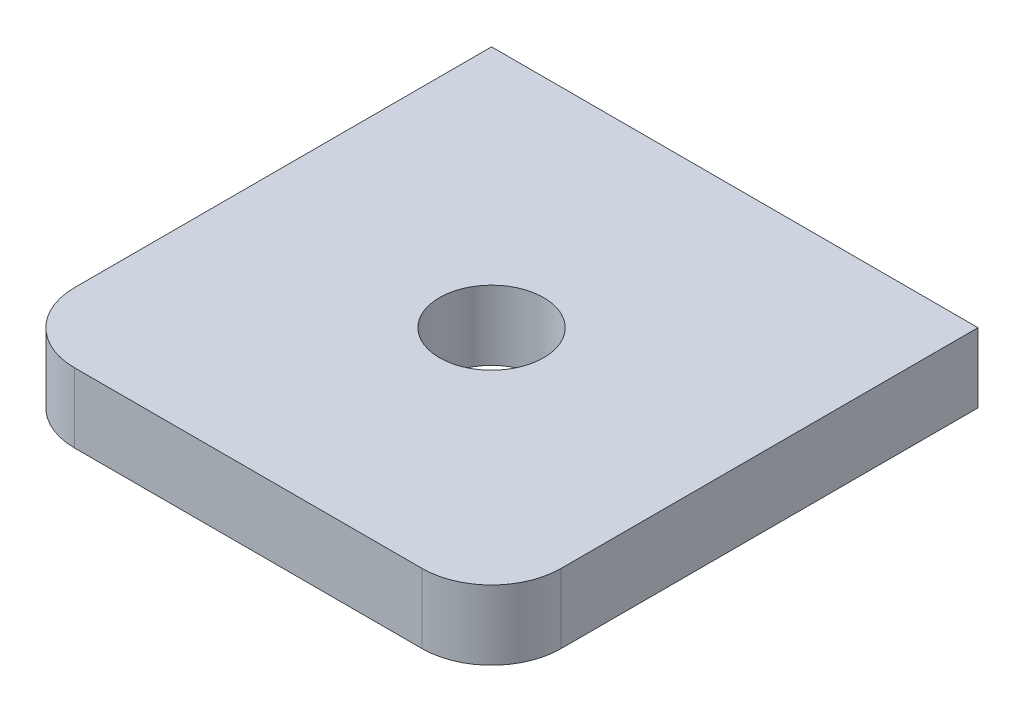
SolidWorks part; units mm, degrees
ref_plane "Alzado" through (0, 0, 0) normal (0, 0, 1) x (1, 0, 0)
ref_plane "Planta" through (0, 0, 0) normal (0, 1, 0) x (1, 0, 0)
ref_plane "Vista lateral" through (0, 0, 0) normal (1, 0, 0) x (0, 0, -1)
sketch "Croquis1" plane through (0, 0, 0) normal (0, 1, 0) x (1, 0, 0)
  line L1 (-35, 35) -> (35, 35)
  line L2 (-35, 35) -> (-35, -25)
  line L3 (-25, -35) -> (25, -35)
  line L4 (35, 35) -> (35, -25)
  line L5 (-35, 35) -> (35, -35) construction
  line L6 (-35, -35) -> (35, 35) construction
  circle A0 centre (0, 0) radius 7.5
  arc A1 (35, -25) -> (25, -35) centre (25, -25) cw
  arc A2 (-25, -35) -> (-35, -25) centre (-25, -25) cw
  point P0 (0, 0)
  dimension "D1" = 15
  dimension "D2" = 10
  dimension "D3" = 35
  dimension "D4" = 35
extrude "Saliente-Extruir1" add sketch "Croquis1" along normal blind 10
